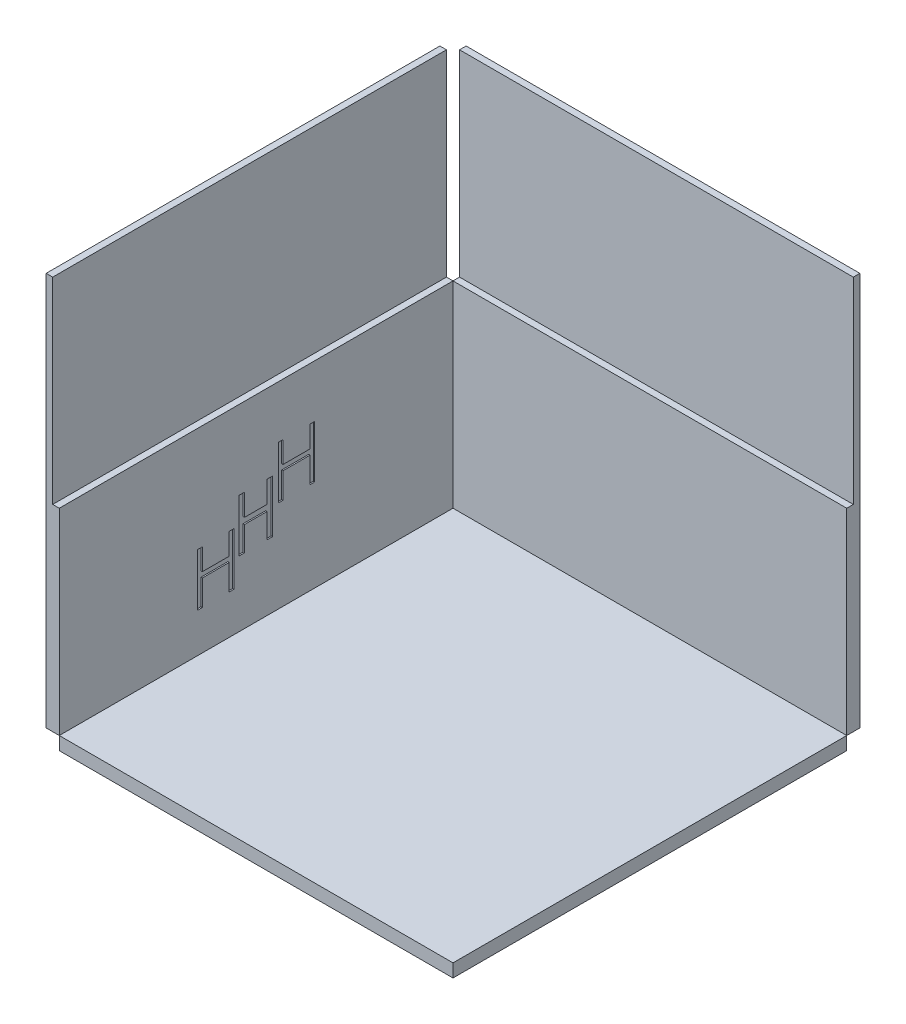
SolidWorks part; units mm, degrees
ref_plane "Front Plane" through (0, 0, 0) normal (0, 0, 1) x (1, 0, 0)
ref_plane "Top Plane" through (0, 0, 0) normal (0, 1, 0) x (1, 0, 0)
ref_plane "Right Plane" through (0, 0, 0) normal (1, 0, 0) x (0, 0, -1)
sketch "Sketch1" plane through (0, 0, 0) normal (0, 1, 0) x (1, 0, 0)
  line L1 (0, 0) -> (300, 0)
  line L2 (0, 0) -> (0, 300)
  line L3 (0, 300) -> (300, 300)
  line L4 (300, 0) -> (300, 300)
  dimension "D1" = 300
  dimension "D2" = 300
extrude "Boss-Extrude1" add sketch "Sketch1" against normal blind 10
sketch "Sketch2" plane through (0, 0, 0) normal (1, 0, 0) x (0, 0, -1)
  line L1 (0, 0) -> (300, 0)
  line L2 (0, 0) -> (0, 150)
  line L3 (0, 150) -> (300, 150)
  line L4 (300, 0) -> (300, 150)
  dimension "D1" = 150
extrude "Boss-Extrude2" add sketch "Sketch2" against normal blind 10 separate body
sketch "Sketch3" plane through (0, 0, 0) normal (0, 0, 1) x (1, 0, 0)
  line L1 (0, 0) -> (300, 0)
  line L2 (0, 0) -> (0, 150)
  line L3 (0, 150) -> (300, 150)
  line L4 (300, 0) -> (300, 150)
extrude "Boss-Extrude3" add sketch "Sketch3" against normal blind 10 from surface at -300 separate body starting at face at (150, -5, -300)
sketch "Sketch4" plane through (0, 150, 0) normal (0, 1, 0) x (1, 0, 0)
  line L0 (-10, 300) -> (0, 300) construction
  line L1 (-10, 0) -> (-5, 0)
  line L2 (-10, 0) -> (-10, 300)
  line L3 (-10, 300) -> (-5, 300)
  line L4 (-5, 0) -> (-5, 300)
  line L5 (300, 310) -> (300, 300) construction
  line L6 (0, 310) -> (300, 310)
  line L7 (0, 310) -> (0, 305)
  line L8 (0, 305) -> (300, 305)
  line L9 (300, 310) -> (300, 305)
extrude "Boss-Extrude4" add sketch "Sketch4" along normal offset from surface (150 mm away) 300 up to face at (150, 0, -150) offset beyond the face yes
sketch "Sketch5" plane through (0, 0, 0) normal (1, 0, 0) x (0, 0, -1)
  line L0 (0, 70) -> (300, 70) construction
  line L1 (0, 150) -> (0, 0) construction
  line L2 (300, 150) -> (300, 0) construction
  line L3 (0, 0) -> (300, 0) construction
  line L4 (0, 50) -> (300, 50) construction
  line L5 (300, 0) -> (300, 150) construction
  line L6 (0, 30) -> (300, 30) construction
  text T0 "H" font "Arial Narrow" height 40
  text T1 "H    " font "Century Gothic" height 40
  text T2 "    H" font "Century Gothic" height 40
  dimension "D1" = 70
  dimension "D2" = 20
  dimension "D3" = 20
extrude "Cut-Extrude1" cut sketch "Sketch5" against normal blind 1
